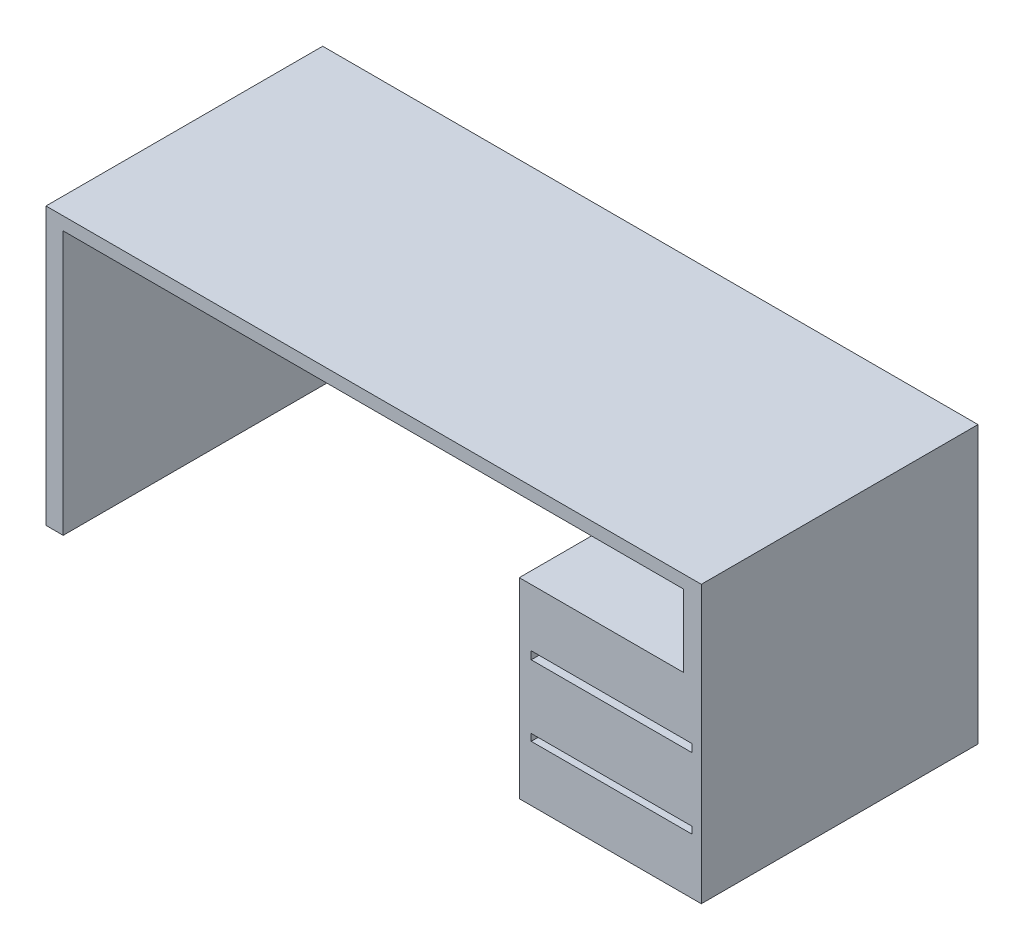
SolidWorks part; units mm, degrees
ref_plane "Alzado" through (0, 0, 0) normal (0, 0, 1) x (1, 0, 0)
ref_plane "Planta" through (0, 0, 0) normal (0, 1, 0) x (1, 0, 0)
ref_plane "Vista lateral" through (0, 0, 0) normal (1, 0, 0) x (0, 0, -1)
sketch "Croquis2" plane through (0, 0, 0) normal (0, 0, 1) x (1, 0, 0)
  line L0 (0, 0) -> (0, 760)
  line L1 (0, 760) -> (1800, 760)
  line L2 (1800, 760) -> (1800, 0)
  line L3 (1800, 0) -> (1300, 0)
  line L4 (1300, 0) -> (1300, 525.8459)
  line L5 (1300, 525.8459) -> (1750.4679, 525.8459)
  line L6 (1750.4679, 525.8459) -> (1750.4679, 724.3194)
  line L7 (1750.4679, 724.3194) -> (47.2137, 724.3194)
  line L8 (47.2137, 724.3194) -> (47.2137, 0)
  line L9 (47.2137, 0) -> (0, 0)
  dimension "D1" = 760
  dimension "D2" = 1800
  dimension "D3" = 500
extrude "Saliente-Extruir1" add sketch "Croquis2" along normal blind 760
sketch "Croquis3" plane through (0, 0, 760) normal (0, 0, 1) x (1, 0, 0)
  line L1 (1332.7555, 368.3015) -> (1774.526, 368.3015)
  line L2 (1332.7555, 368.3015) -> (1332.7555, 346.7517)
  line L3 (1332.7555, 346.7517) -> (1774.526, 346.7517)
  line L4 (1774.526, 368.3015) -> (1774.526, 346.7517)
  line L5 (1332.7555, 171.6598) -> (1774.526, 171.6598)
  line L6 (1332.7555, 171.6598) -> (1332.7555, 152.8037)
  line L7 (1332.7555, 152.8037) -> (1774.526, 152.8037)
  line L8 (1774.526, 171.6598) -> (1774.526, 152.8037)
extrude "Cortar-Extruir1" cut sketch "Croquis3" against normal blind 899
